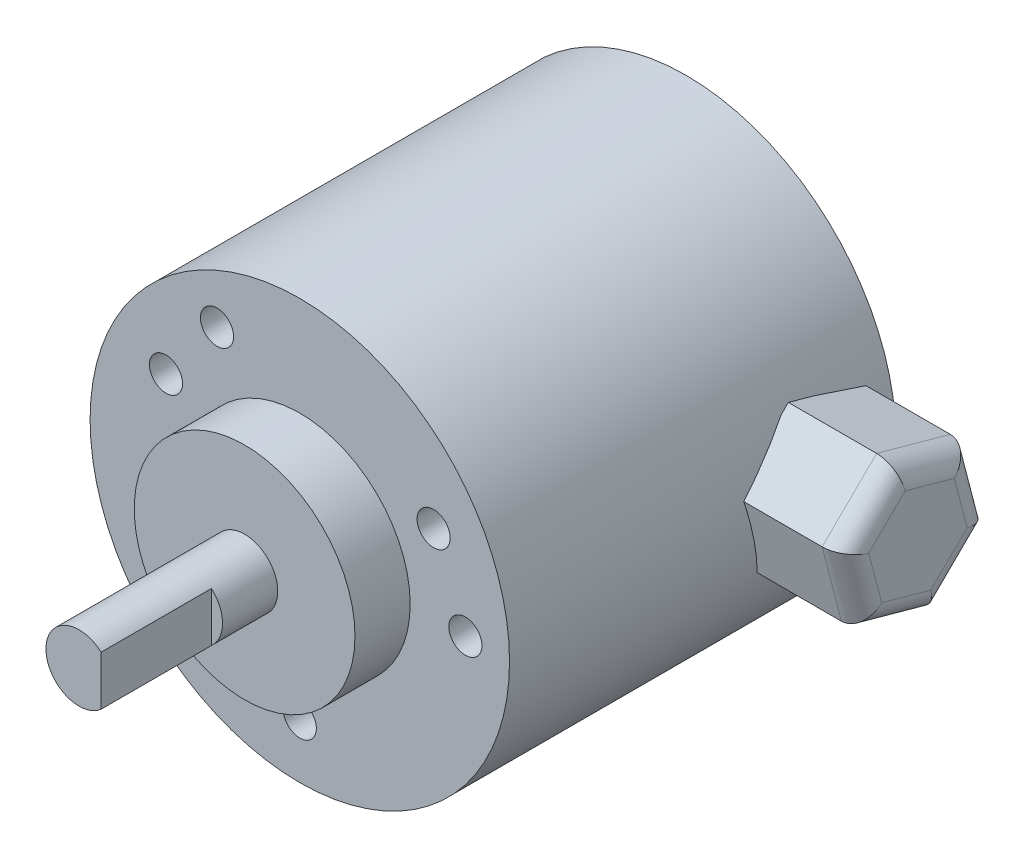
SolidWorks part; units mm, degrees
ref_plane "Front Plane" through (0, 0, 0) normal (0, 0, 1) x (1, 0, 0)
ref_plane "Top Plane" through (0, 0, 0) normal (0, 1, 0) x (1, 0, 0)
ref_plane "Right Plane" through (0, 0, 0) normal (1, 0, 0) x (0, 0, -1)
sketch "Sketch3" plane through (0, 0, 0) normal (0, 0, 1) x (1, 0, 0)
  circle A0 centre (0, 0) radius 19
  dimension "D1" = 38
extrude "Boss-Extrude1" add sketch "Sketch3" along normal blind 40
sketch "Sketch4" plane through (0, 0, 40) normal (0, 0, 1) x (1, 0, 0)
  circle A0 centre (0, 0) radius 10
  circle A1 centre (0, 0) radius 19
  dimension "D1" = 20
extrude "Cut-Extrude1" cut sketch "Sketch4" against normal blind 5
sketch "Sketch6" plane through (0, 0, 35) normal (0, 0, 1) x (1, 0, 0)
  line L0 (0, 0) -> (19, 0) construction
  line L1 (0, 0) -> (12.1244, 7) construction
  circle A0 centre (0, 0) radius 19 construction
  circle A1 centre (15, 0) radius 1.5
  circle A2 centre (0, 0) radius 15 construction
  circle A3 centre (0, 0) radius 14 construction
  circle A4 centre (-7.5, -12.9904) radius 1.5
  circle A5 centre (-7.5, 12.9904) radius 1.5
  circle A6 centre (12.1244, 7) radius 1.5
  circle A7 centre (-12.1244, 7) radius 1.5
  circle A8 centre (0, -14) radius 1.5
  dimension "D1" = 3
  dimension "D2" = 30
  dimension "D3" = 28
  dimension "D4" = 120
  dimension "D6" = 30
  dimension "D5" = 120
  dimension "D7" = 120
  dimension "D8" = 120
extrude "Cut-Extrude2" cut sketch "Sketch6" against normal blind 6.6
sketch "Sketch10" plane through (0, 0, 40) normal (0, 0, 1) x (1, 0, 0)
  line L0 (0, 0) -> (10, 0) construction
  circle A0 centre (0, 0) radius 10 construction
  point P0 (0, 0)
sketch "Sketch5" plane through (0, 0, 40) normal (0, 0, 1) x (1, 0, 0)
  circle A0 centre (0, 0) radius 3
  dimension "D1" = 6
extrude "Boss-Extrude2" add sketch "Sketch5" along normal blind 15
sketch "Sketch7" plane through (0, 0, 0) normal (0, 0, -1) x (-1, 0, 0)
  line L0 (0, 0) -> (-19, 0) construction
  circle A0 centre (0, 0) radius 19 construction
ref_plane "Plane1" through (19, 0, 0) normal (1, 0, 0) x (0, 0, -1)
sketch "Sketch8" plane through (19, 0, 0) normal (1, 0, 0) x (0, 0, -1)
  line L1 (-2.0636, 4.8612) -> (-8.7417, 6.7057)
  line L2 (-8.7417, 6.7057) -> (-13.6782, 1.8445)
  line L3 (-13.6782, 1.8445) -> (-11.9364, -4.8612)
  line L4 (-11.9364, -4.8612) -> (-5.2583, -6.7057)
  line L5 (-5.2583, -6.7057) -> (-0.3218, -1.8445)
  line L6 (-0.3218, -1.8445) -> (-2.0636, 4.8612)
  circle A0 centre (-7, 0) radius 6 construction
  dimension "D1" = 7
  dimension "D2" = 12
extrude "Boss-Extrude3" add sketch "Sketch8" along normal blind 9 and the other way blind 1 separate body
fillet "Fillet1" radius 2 6 edges at (28, 1.5084, 1.1927) (28, -4.2751, 2.7901) (28, -5.7835, 8.5974) (28, -1.5084, 12.8073) (28, 4.2751, 11.2099) (28, 5.7835, 5.4026)
sketch "Sketch9" plane through (0, 0, 55) normal (0, 0, 1) x (1, 0, 0)
  line L0 (2, 2.2361) -> (2, -2.2361)
  line L1 (0, -3) -> (0, 3) construction
  circle A0 centre (0, 0) radius 3 construction
  arc A1 (2, 2.2361) -> (2, -2.2361) centre (0, 0) cw
  point P9 (0, 0)
  dimension "D1" = 2
extrude "Cut-Extrude3" cut sketch "Sketch9" against normal blind 10
sketch "Sketch11" plane through (0, 0, 0) normal (0, 1, 0) x (1, 0, 0)
  line L0 (0, -40) -> (0, -47.5) construction
  dimension "D1" = 7.5
